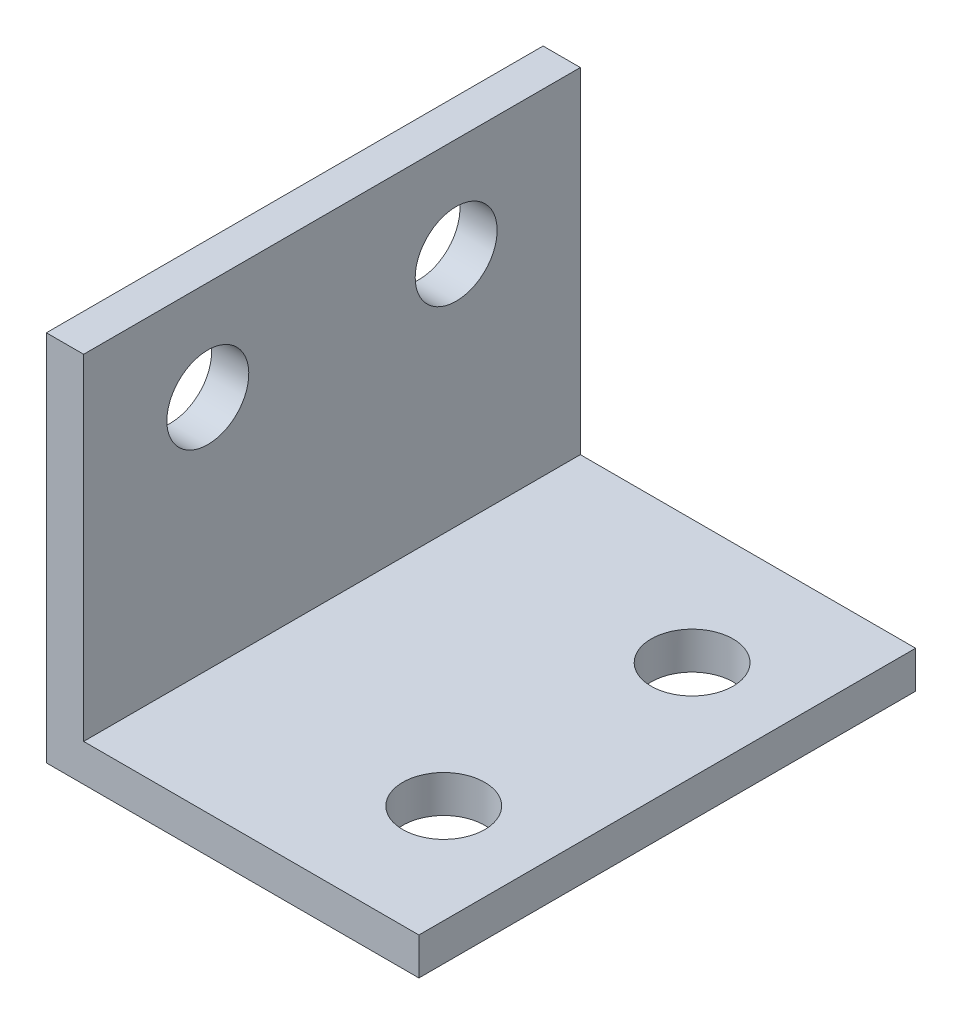
SolidWorks part; units mm, degrees
material "1.0503 (C45)"
ref_plane "前视基准面" through (0, 0, 0) normal (0, 0, 1) x (1, 0, 0)
ref_plane "上视基准面" through (0, 0, 0) normal (0, 1, 0) x (1, 0, 0)
ref_plane "右视基准面" through (0, 0, 0) normal (1, 0, 0) x (0, 0, -1)
sketch "草图1" plane through (0, 0, 0) normal (0, 0, 1) x (1, 0, 0)
  line L0 (0, 0) -> (0, 30)
  line L1 (0, 30) -> (3, 30)
  line L2 (3, 30) -> (3, 3)
  line L3 (3, 3) -> (30, 3)
  line L4 (30, 3) -> (30, 0)
  line L5 (30, 0) -> (0, 0)
  dimension "D1" = 3
  dimension "D2" = 3
  dimension "D3" = 30
  dimension "D4" = 30
extrude "凸台-拉伸1" add sketch "草图1" along normal blind 40
sketch "草图2" plane through (0, 0, 0) normal (-1, 0, 0) x (0, 0, 1)
  line L0 (20, 30) -> (20, 6.056) construction
  line L1 (40, 30) -> (0, 30) construction
  circle A0 centre (10, 22) radius 3.3
  circle A1 centre (30, 22) radius 3.3
  dimension "D1" = 6.6
  dimension "D2" = 10
  dimension "D3" = 8
extrude "切除-拉伸1" cut sketch "草图2" against normal blind 40
sketch "草图3" plane through (0, 0, 0) normal (0, -1, 0) x (1, 0, 0)
  line L0 (0, 20) -> (30, 20) construction
  line L1 (0, 40) -> (0, 0) construction
  line L2 (30, 40) -> (30, 0) construction
  circle A0 centre (22, 30) radius 3.3
  circle A1 centre (22, 10) radius 3.3
  dimension "D1" = 6.6
  dimension "D3" = 8
  dimension "D2" = 10
extrude "切除-拉伸2" cut sketch "草图3" against normal blind 40
